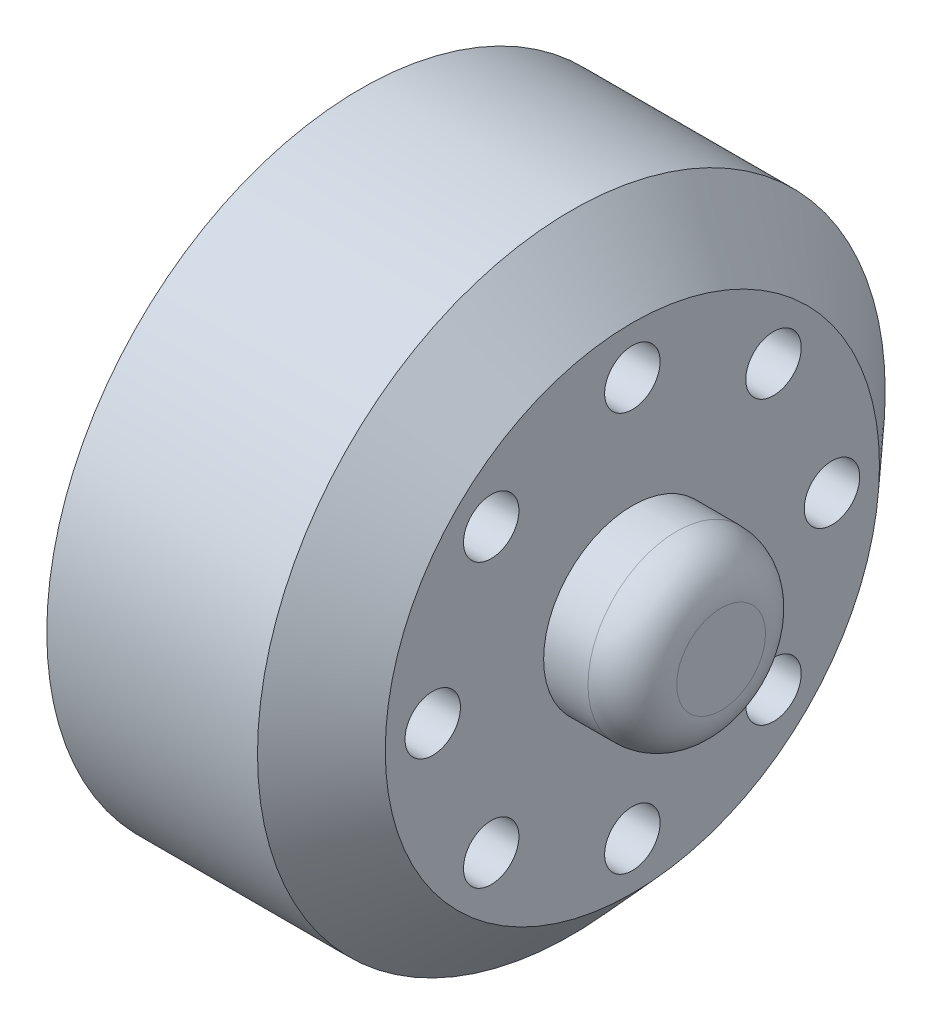
SolidWorks part; units mm, degrees
ref_plane "Front Plane" through (0, 0, 0) normal (0, 0, 1) x (1, 0, 0)
ref_plane "Top Plane" through (0, 0, 0) normal (0, 1, 0) x (1, 0, 0)
ref_plane "Right Plane" through (0, 0, 0) normal (1, 0, 0) x (0, 0, -1)
sketch "Sketch1" plane through (0, 0, 0) normal (0, 1, 0) x (1, 0, 0)
  line L0 (-12.3913, 0) -> (21, 0) construction
  line L1 (-1.6304, 14.15) -> (7.8696, 14.15)
  line L5 (13.3727, 0) -> (5.3696, 0)
  line L8 (10.6196, 4) -> (14.6196, 4)
  line L9 (14.6196, 4) -> (14.6196, 0)
  line L10 (14.6196, 0) -> (13.3727, 0)
  line L15 (7.8696, 14.15) -> (10.6196, 11.1405)
  line L17 (10.6196, 11.1405) -> (10.6196, 4)
  line L18 (-1.6304, 14.15) -> (-1.6304, 10.5)
  line L20 (5.3696, 10.5) -> (5.3696, 0)
  line L21 (5.3696, 10.5) -> (-1.6304, 10.5)
  dimension "D2" = 132.42
  dimension "D3" = 4.0767
  dimension "D4" = 9.5
  dimension "D5" = 28.3
  dimension "D6" = 3.0095
  dimension "D7" = 4
  dimension "D8" = 8
  dimension "D9" = 7
  dimension "D10" = 21
  dimension "D11" = 11.1405
  dimension "D12" = 12.25
revolve "Revolve1" add sketch "Sketch1" angle 360 about L0
fillet "Fillet1" radius 2 1 edges at (14.6196, 0, 4)
sketch "Sketch2" plane through (10.6196, 0, 0) normal (1, 0, 0) x (0, 0, -1)
  circle A0 centre (0, 0) radius 9 construction
  circle A1 centre (0, 9) radius 1.25
  circle A2 centre (6.364, 6.364) radius 1.25
  circle A3 centre (9, 0) radius 1.25
  circle A4 centre (6.364, -6.364) radius 1.25
  circle A5 centre (0, -9) radius 1.25
  circle A6 centre (-6.364, -6.364) radius 1.25
  circle A7 centre (-9, 0) radius 1.25
  circle A8 centre (-6.364, 6.364) radius 1.25
  point P22 (0, 0)
  dimension "D1" = 18
  dimension "D2" = 2.5
  dimension "D3" = 8
extrude "Cut-Extrude1" cut sketch "Sketch2" against normal up to surface (12.25 mm away) up to face at (-1.6304, 0, 10.5)
sketch "Sketch3" plane through (-1.6304, 0, 0) normal (-1, 0, 0) x (0, 0, 1)
  circle A0 centre (0, 0) radius 9 construction
  circle A1 centre (0, 9) radius 2.5
  circle A2 centre (6.364, 6.364) radius 2.5
  circle A3 centre (9, 0) radius 2.5
  circle A4 centre (6.364, -6.364) radius 2.5
  circle A5 centre (0, -9) radius 2.5
  circle A6 centre (-6.364, -6.364) radius 2.5
  circle A7 centre (-9, 0) radius 2.5
  circle A8 centre (-6.364, 6.364) radius 2.5
  point P22 (0, 0)
  dimension "D1" = 18
  dimension "D2" = 5
  dimension "D3" = 8
extrude "Cut-Extrude2" cut sketch "Sketch3" against normal offset from surface (7.25 mm away) 5 up to face at (10.6196, 9, -1.25)
